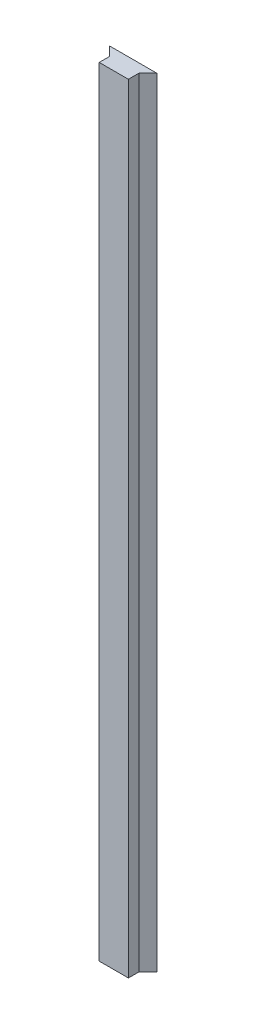
SolidWorks part; units mm, degrees
ref_plane "Front Plane" through (0, 0, 0) normal (0, 0, 1) x (1, 0, 0)
ref_plane "Top Plane" through (0, 0, 0) normal (0, 1, 0) x (1, 0, 0)
ref_plane "Right Plane" through (0, 0, 0) normal (1, 0, 0) x (0, 0, -1)
sketch "Sketch1" plane through (0, 0, 0) normal (0, 1, 0) x (1, 0, 0)
  line L0 (0, 0) -> (19.05, 0)
  line L1 (19.05, 0) -> (19.05, 6.858)
  line L2 (19.05, 6.858) -> (24.892, 12.7)
  line L3 (24.892, 12.7) -> (-5.842, 12.7)
  line L4 (-5.842, 12.7) -> (0, 6.858)
  line L5 (0, 6.858) -> (0, 0)
  dimension "D1" = 12.7
  dimension "D2" = 45
  dimension "D3" = 19.05
  dimension "D4" = 6.858
  dimension "D5" = 30.734
  dimension "D6" = 6.858
extrude "Boss-Extrude1" add sketch "Sketch1" along normal blind 508
